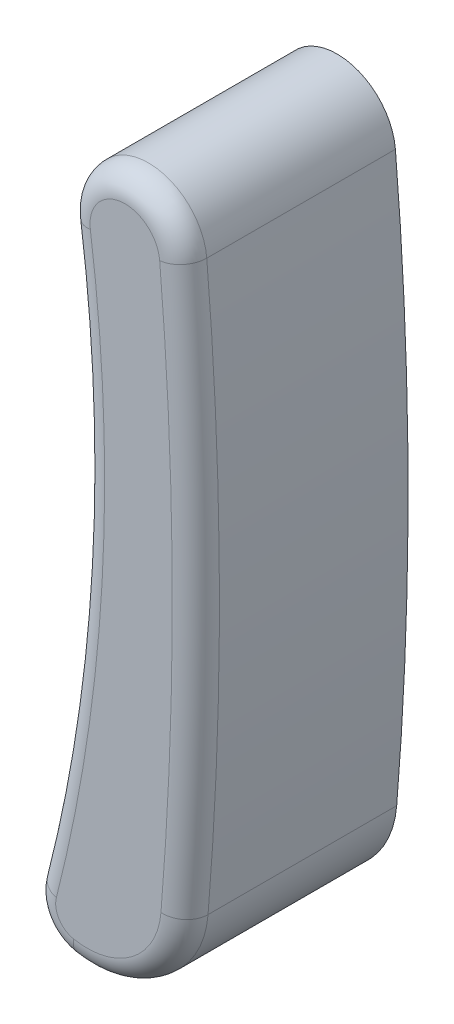
SolidWorks part; units mm, degrees
ref_plane "前视基准面" through (0, 0, 0) normal (0, 0, 1) x (1, 0, 0)
ref_plane "上视基准面" through (0, 0, 0) normal (0, 1, 0) x (1, 0, 0)
ref_plane "右视基准面" through (0, 0, 0) normal (1, 0, 0) x (0, 0, -1)
sketch "Sketch2" plane through (0, 0, 0) normal (0, 0, 1) x (1, 0, 0)
  arc A5 (1.4676, 6.4041) -> (-0.9967, 6.1288) centre (0.2321, 6.2964) ccw
  arc A6 (-1.7065, -6.3121) -> (-0.9967, 6.1288) centre (-33.2472, 1.728) ccw
  arc A7 (-1.7065, -6.3121) -> (-0.9461, -7.5018) centre (-0.7694, -6.551) ccw
  arc A8 (-0.9461, -7.5018) -> (1.495, -5.637) centre (-0.5679, -5.4667) ccw
  arc A9 (1.495, -5.637) -> (1.4676, 6.4041) centre (-69.4738, 0.2221) ccw
extrude "Extrude1" add sketch "Sketch2" along normal blind 4.5
fillet "Fillet1" radius 0.5 5 edges at (0.6887, -7.1116, 4.5) (-1.5842, -7.0719, 4.5) (-0.7507, -0.126, 4.5) (0.0944, 7.529, 4.5) (1.7363, 0.3841, 4.5)
